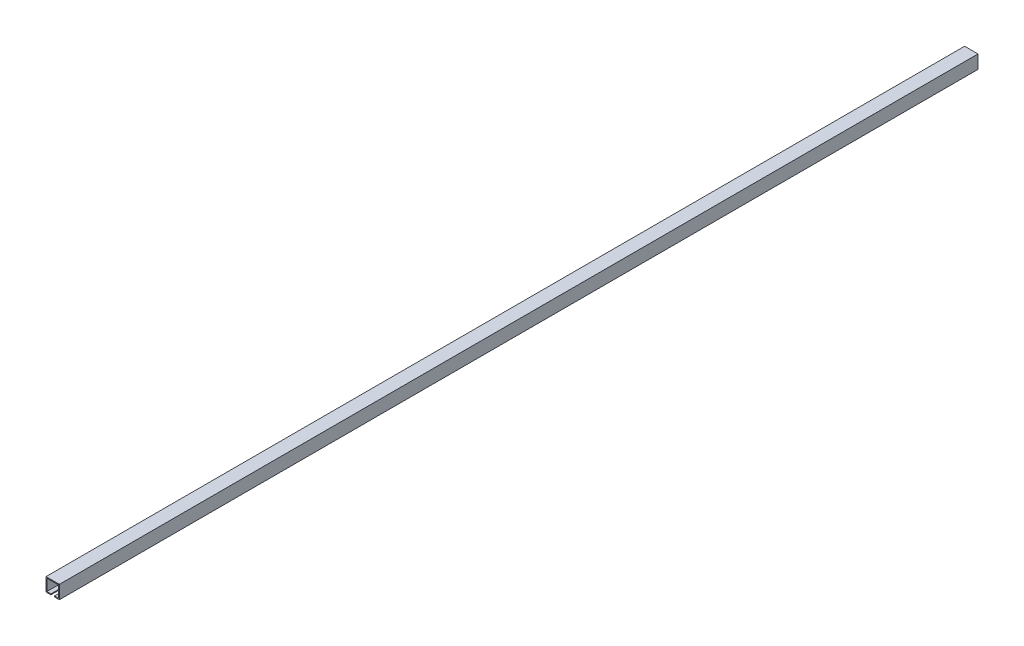
SolidWorks part; units mm, degrees
ref_plane "Front Plane" through (0, 0, 0) normal (0, 0, 1) x (1, 0, 0)
ref_plane "Top Plane" through (0, 0, 0) normal (0, 1, 0) x (1, 0, 0)
ref_plane "Right Plane" through (0, 0, 0) normal (1, 0, 0) x (0, 0, -1)
sketch "Sketch1" plane through (0, 0, 0) normal (0, 0, 1) x (1, 0, 0)
  line L0 (-4, -13) -> (-4, -15)
  line L1 (-4, -15) -> (-15, -15)
  line L2 (-15, -15) -> (-15, 15)
  line L3 (-15, 15) -> (15, 15)
  line L4 (15, 15) -> (15, -15)
  line L5 (15, -15) -> (4, -15)
  line L6 (4, -15) -> (4, -13)
  line L7 (4, -13) -> (13, -13)
  line L8 (13, -13) -> (13, 13)
  line L9 (13, 13) -> (-13, 13)
  line L10 (-13, 13) -> (-13, -13)
  line L11 (-13, -13) -> (-4, -13)
  point P13 (0, 13)
  point P14 (-13, 0)
  dimension "D1" = 30
  dimension "D2" = 30
  dimension "D3" = 2
  dimension "D4" = 2
  dimension "D5" = 2
  dimension "D6" = 2
  dimension "D7" = 9
extrude "Boss-Extrude1" add sketch "Sketch1" along normal mid plane 2060
